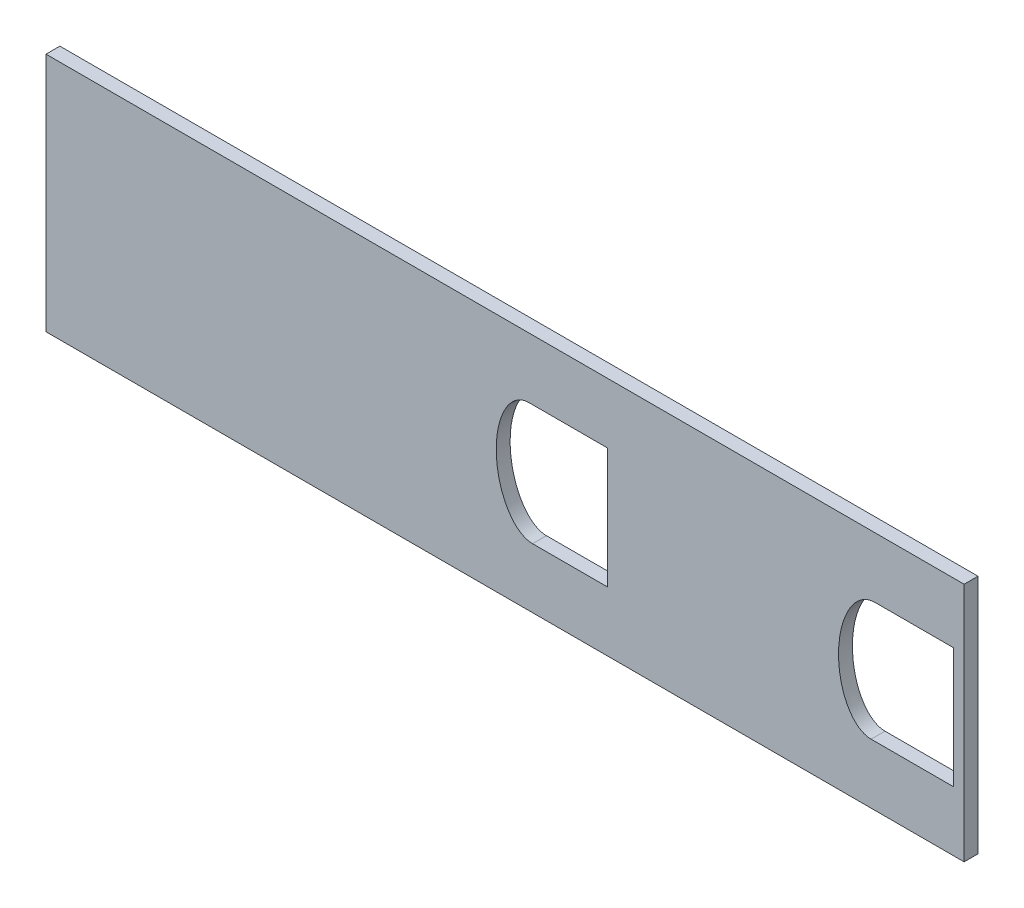
SolidWorks part; units mm, degrees
material "FiberBoard"
ref_plane "Front Plane" through (0, 0, 0) normal (0, 0, 1) x (1, 0, 0)
ref_plane "Top Plane" through (0, 0, 0) normal (0, 1, 0) x (1, 0, 0)
ref_plane "Right Plane" through (0, 0, 0) normal (1, 0, 0) x (0, 0, -1)
sketch "Sketch1" plane through (0, 0, 0) normal (0, 0, 1) x (1, 0, 0)
  line L0 (-366.5883, 451.6829) -> (-366.5883, -259.5171) construction
  line L1 (-360.2383, -143.6167) -> (-169.5684, -143.6167) construction
  line L2 (-366.5883, 451.6829) -> (-366.5883, -259.5171) construction
  line L3 (-366.5883, -143.6167) -> (-169.5684, -143.6167) construction
  line L4 (-256.1265, -129.9145) -> (-238.1265, -129.9145)
  line L5 (-366.5883, -171.1167) -> (-156.5883, -171.1167)
  line L6 (-366.5883, -171.1167) -> (-366.5883, -116.1167)
  line L7 (-366.5883, -116.1167) -> (-156.5883, -116.1167)
  line L8 (-156.5883, -171.1167) -> (-156.5883, -116.1167)
  line L9 (-238.1265, -129.9145) -> (-238.1265, -157.4451)
  line L10 (-238.1265, -157.4451) -> (-255.3019, -157.4451)
  line L11 (-177.0405, -129.9145) -> (-159.0405, -129.9145)
  line L12 (-159.0405, -129.9145) -> (-159.0405, -157.4451)
  line L13 (-159.0405, -157.4451) -> (-177.8647, -157.4451)
  spline S0 degree 3 poles (-176.654, -129.9161) (-177.3873, -129.913) (-177.7464, -129.955) (-178.4505, -130.1183) (-178.7984, -130.2415) (-179.7841, -130.7032) (-180.3818, -131.1387) (-181.1687, -131.8804) (-181.4148, -132.1437) (-181.8798, -132.6969) (-182.0996, -132.9883) (-182.7148, -133.884) (-183.0678, -134.5099) (-183.689, -135.8042) (-183.9567, -136.4729) (-184.4188, -137.8471) (-184.6092, -138.5407) (-185.0765, -140.6374) (-185.2511, -142.0564) (-185.3284, -144.2137) (-185.3226, -144.9395) (-185.2455, -146.3731) (-185.1745, -147.0841) (-184.9634, -148.4938) (-184.8233, -149.1925) (-184.4639, -150.5759) (-184.2446, -151.2611) (-183.7058, -152.6115) (-183.3919, -153.2634) (-182.8329, -154.1954) (-182.6306, -154.4998) (-182.1971, -155.0794) (-181.9659, -155.3553) (-181.4687, -155.874) (-181.2029, -156.1167) (-180.7711, -156.4492) (-180.6208, -156.5551) (-180.3134, -156.7507) (-180.1559, -156.8409) (-179.8328, -157.0045) (-179.6672, -157.0781) (-179.327, -157.2069) (-179.1511, -157.2625) (-178.6209, -157.3961) (-178.2628, -157.4422) (-177.7187, -157.4464) (-177.535, -157.4369) (-177.1717, -157.3961) (-176.9927, -157.365) (-176.6395, -157.2831) (-176.4654, -157.2323) (-176.1218, -157.1117) (-175.9515, -157.0416) (-175.4569, -156.8091) (-175.1462, -156.6244) (-174.5549, -156.2074) (-174.2726, -155.9733) (-173.4799, -155.225) (-173.0218, -154.6688) (-172.4067, -153.7757) (-172.2133, -153.4667) (-171.8523, -152.8376) (-171.6848, -152.5179) (-171.2159, -151.5458) (-170.9477, -150.8801) (-170.485, -149.52) (-170.2903, -148.824) (-169.8098, -146.7052) (-169.6319, -145.2841) (-169.5488, -143.1415) (-169.5521, -142.4255) (-169.6251, -140.9894) (-169.6955, -140.2658) (-169.908, -138.8383) (-170.0497, -138.1335) (-170.4129, -136.7438) (-170.6342, -136.0589) (-171.0408, -135.0502) (-171.1887, -134.7178) (-171.5089, -134.0696) (-171.6816, -133.7528) (-172.0561, -133.1361) (-172.2578, -132.8361) (-172.6966, -132.2566) (-172.9326, -131.9788) (-173.4365, -131.4614) (-173.7051, -131.2203) (-174.2843, -130.7823) (-174.595, -130.5862) (-175.2423, -130.2646) (-175.5839, -130.1362) (-176.2934, -129.9612) (-176.654, -129.9161) (-177.3873, -129.913) (-177.7464, -129.955) knots -0.015625 -0.015625 0 0 0.015625 0.015625 0.03125 0.03125 0.0625 0.0625 0.078125 0.078125 0.09375 0.09375 0.125 0.125 0.15625 0.15625 0.1875 0.1875 0.25 0.25 0.28125 0.28125 0.3125 0.3125 0.34375 0.34375 0.375 0.375 0.40625 0.40625 0.421875 0.421875 0.4375 0.4375 0.453125 0.453125 0.460937 0.460937 0.46875 0.46875 0.476562 0.476562 0.484375 0.484375 0.5 0.5 0.507812 0.507812 0.515625 0.515625 0.523437 0.523437 0.53125 0.53125 0.546875 0.546875 0.5625 0.5625 0.59375 0.59375 0.609375 0.609375 0.625 0.625 0.65625 0.65625 0.6875 0.6875 0.75 0.75 0.78125 0.78125 0.8125 0.8125 0.84375 0.84375 0.875 0.875 0.890625 0.890625 0.90625 0.90625 0.921875 0.921875 0.9375 0.9375 0.953125 0.953125 0.96875 0.96875 0.984375 0.984375 1 1 1.015625 1.015625 1.03125 only from (-177.0206, -129.9145) to (-177.0206, -129.9145) construction
  spline S1 degree 3 poles (-255.779, -129.913) (-256.5129, -129.9161) (-256.872, -129.9613) (-257.5751, -130.1339) (-257.9216, -130.2634) (-258.5716, -130.5862) (-258.8795, -130.7802) (-259.4628, -131.2212) (-259.7319, -131.4631) (-260.2351, -131.9801) (-260.469, -132.2554) (-260.9073, -132.8339) (-261.1113, -133.1372) (-261.6736, -134.0637) (-261.9883, -134.71) (-262.5275, -136.0456) (-262.7525, -136.7394) (-263.1172, -138.1345) (-263.2582, -138.8377) (-263.4694, -140.2535) (-263.5395, -140.9662) (-263.6139, -142.4005) (-263.6181, -143.1251) (-263.535, -145.2889) (-263.355, -146.7101) (-262.8805, -148.8068) (-262.6879, -149.4998) (-262.2222, -150.8721) (-261.9518, -151.5434) (-261.4822, -152.5171) (-261.3149, -152.8364) (-260.9554, -153.4631) (-260.7625, -153.7716) (-260.146, -154.6674) (-259.688, -155.2232) (-258.8998, -155.9681) (-258.6177, -156.2027) (-258.0261, -156.6209) (-257.7157, -156.8057) (-257.2232, -157.0381) (-257.0535, -157.1083) (-256.7104, -157.2294) (-256.5367, -157.2805) (-256.185, -157.3629) (-256.007, -157.3942) (-255.6464, -157.4357) (-255.4625, -157.446) (-254.9169, -157.4434) (-254.559, -157.3982) (-254.0306, -157.2669) (-253.855, -157.2121) (-253.5141, -157.0842) (-253.3481, -157.0112) (-252.8627, -156.7671) (-252.5529, -156.5691) (-251.9766, -156.1279) (-251.7097, -155.8854) (-251.2097, -155.3657) (-250.9759, -155.0875) (-250.5398, -154.5053) (-250.3398, -154.2047) (-249.7836, -153.2798) (-249.4707, -152.6327) (-249.0673, -151.6272) (-248.9438, -151.2851) (-248.72, -150.5985) (-248.6193, -150.2532) (-248.3475, -149.212) (-248.2062, -148.5107) (-247.9933, -147.0957) (-247.9217, -146.3821) (-247.844, -144.9431) (-247.8382, -144.2186) (-247.9148, -142.0655) (-248.0885, -140.6446) (-248.558, -138.5378) (-248.7509, -137.8372) (-249.2105, -136.4719) (-249.4773, -135.8046) (-250.1003, -134.5069) (-250.4593, -133.872) (-251.2765, -132.6843) (-251.7338, -132.1288) (-252.793, -131.1315) (-253.3784, -130.7051) (-254.3701, -130.2406) (-254.7107, -130.12) (-255.4142, -129.9559) (-255.779, -129.913) (-256.5129, -129.9161) (-256.872, -129.9613) knots -0.015625 -0.015625 0 0 0.015625 0.015625 0.03125 0.03125 0.046875 0.046875 0.0625 0.0625 0.078125 0.078125 0.09375 0.09375 0.125 0.125 0.15625 0.15625 0.1875 0.1875 0.21875 0.21875 0.25 0.25 0.3125 0.3125 0.34375 0.34375 0.375 0.375 0.390625 0.390625 0.40625 0.40625 0.4375 0.4375 0.453125 0.453125 0.46875 0.46875 0.476563 0.476563 0.484375 0.484375 0.492188 0.492188 0.5 0.5 0.515625 0.515625 0.523438 0.523438 0.53125 0.53125 0.546875 0.546875 0.5625 0.5625 0.578125 0.578125 0.59375 0.59375 0.625 0.625 0.640625 0.640625 0.65625 0.65625 0.6875 0.6875 0.71875 0.71875 0.75 0.75 0.8125 0.8125 0.84375 0.84375 0.875 0.875 0.90625 0.90625 0.9375 0.9375 0.96875 0.96875 0.984375 0.984375 1 1 1.015625 1.015625 1.03125 only from (-256.1459, -129.9145) to (-256.1459, -129.9145) construction
  spline S2 degree 3 poles (-177.0405, -129.9145) (-177.4003, -129.9145) (-177.7527, -129.9564) (-178.4505, -130.1183) (-178.7984, -130.2415) (-179.7841, -130.7032) (-180.3818, -131.1387) (-181.1687, -131.8804) (-181.4148, -132.1437) (-181.8798, -132.6969) (-182.0996, -132.9883) (-182.7148, -133.884) (-183.0678, -134.5099) (-183.689, -135.8042) (-183.9567, -136.4729) (-184.4188, -137.8471) (-184.6092, -138.5407) (-185.0765, -140.6374) (-185.2511, -142.0564) (-185.3284, -144.2137) (-185.3226, -144.9395) (-185.2455, -146.3731) (-185.1745, -147.0841) (-184.9634, -148.4938) (-184.8233, -149.1925) (-184.4639, -150.5759) (-184.2446, -151.2611) (-183.7058, -152.6115) (-183.3919, -153.2634) (-182.8329, -154.1954) (-182.6306, -154.4998) (-182.1971, -155.0794) (-181.9659, -155.3553) (-181.4687, -155.874) (-181.2029, -156.1167) (-180.7711, -156.4492) (-180.6208, -156.5551) (-180.3134, -156.7507) (-179.9984, -156.931) (-179.6672, -157.0781) (-179.327, -157.2069) (-179.1511, -157.2625) (-178.6209, -157.3961) (-178.2628, -157.4422) (-177.8883, -157.4451) (-177.8765, -157.4451) (-177.8647, -157.4451) knots 0.000282 0.000282 0.000282 0.000282 0.015625 0.015625 0.03125 0.03125 0.0625 0.0625 0.078125 0.078125 0.09375 0.09375 0.125 0.125 0.15625 0.15625 0.1875 0.1875 0.25 0.25 0.28125 0.28125 0.3125 0.3125 0.34375 0.34375 0.375 0.375 0.40625 0.40625 0.421875 0.421875 0.4375 0.4375 0.453125 0.453125 0.460937 0.460937 0.46875 0.476562 0.476562 0.484375 0.484375 0.5 0.5 0.500508 0.500508 0.500508 0.500508
  spline S3 degree 3 poles (-256.1265, -129.9145) (-256.133, -129.9145) (-256.1395, -129.9145) (-256.5129, -129.9161) (-256.872, -129.9613) (-257.5751, -130.1339) (-257.9216, -130.2634) (-258.5716, -130.5862) (-258.8795, -130.7802) (-259.4628, -131.2212) (-259.7319, -131.4631) (-260.2351, -131.9801) (-260.469, -132.2554) (-260.9073, -132.8339) (-261.1113, -133.1372) (-261.6736, -134.0637) (-261.9883, -134.71) (-262.5275, -136.0456) (-262.7525, -136.7394) (-263.1172, -138.1345) (-263.2582, -138.8377) (-263.4694, -140.2535) (-263.5395, -140.9662) (-263.6139, -142.4005) (-263.6181, -143.1251) (-263.535, -145.2889) (-263.355, -146.7101) (-262.8805, -148.8068) (-262.6879, -149.4998) (-262.2222, -150.8721) (-261.9518, -151.5434) (-261.4822, -152.5171) (-261.3149, -152.8364) (-260.9554, -153.4631) (-260.7625, -153.7716) (-260.146, -154.6674) (-259.688, -155.2232) (-258.8998, -155.9681) (-258.6177, -156.2027) (-258.0261, -156.6209) (-257.7157, -156.8057) (-257.2232, -157.0381) (-257.0535, -157.1083) (-256.7104, -157.2294) (-256.363, -157.3316) (-256.007, -157.3942) (-255.6534, -157.4349) (-255.4768, -157.4451) (-255.3019, -157.4451) knots 0.999724 0.999724 0.999724 0.999724 1 1 1.015625 1.015625 1.03125 1.03125 1.046875 1.046875 1.0625 1.0625 1.078125 1.078125 1.09375 1.09375 1.125 1.125 1.15625 1.15625 1.1875 1.1875 1.21875 1.21875 1.25 1.25 1.3125 1.3125 1.34375 1.34375 1.375 1.375 1.390625 1.390625 1.40625 1.40625 1.4375 1.4375 1.453125 1.453125 1.46875 1.46875 1.476563 1.476563 1.484375 1.492188 1.492188 1.499695 1.499695 1.499695 1.499695
  point P11 (-366.5883, -143.6167)
  point P18 (-176.4999, -157.2395)
  dimension "D1" = 55
  dimension "D2" = 210
  dimension "D3" = 18
  dimension "D4" = 17.1754
  dimension "D5" = 18
extrude "Boss-Extrude2" add sketch "Sketch1" along normal blind 3.175
